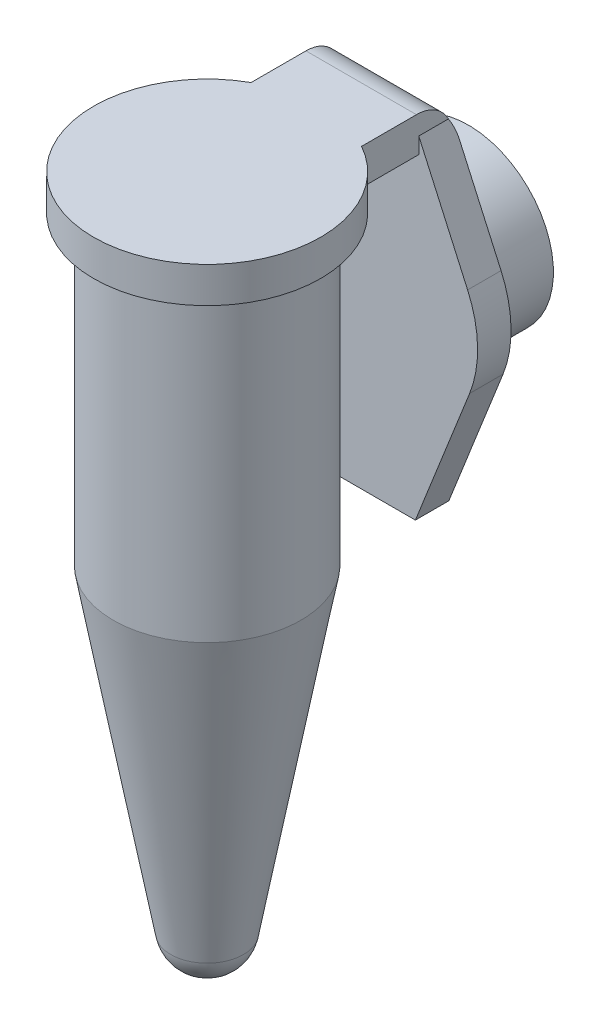
SolidWorks part; units mm, degrees
ref_plane "Front Plane" through (0, 0, 0) normal (0, 0, 1) x (1, 0, 0)
ref_plane "Top Plane" through (0, 0, 0) normal (0, 1, 0) x (1, 0, 0)
ref_plane "Right Plane" through (0, 0, 0) normal (1, 0, 0) x (0, 0, -1)
sketch "Sketch1" plane through (0, 0, 0) normal (0, 0, 1) x (1, 0, 0)
  line L0 (5.25, 36.6) -> (5.25, 19.5)
  line L1 (5.25, 19.5) -> (2.0346, 1.7)
  line L2 (0, 0) -> (0, 38.6)
  line L3 (0, 38.6) -> (6.35, 38.6)
  line L4 (6.35, 38.6) -> (6.35, 36.6)
  line L5 (6.35, 36.6) -> (5.25, 36.6)
  arc A0 (2.0346, 1.7) -> (0, 0) centre (0, 2.0675) cw
  dimension "D1" = 38.6
  dimension "D2" = 2
  dimension "D3" = 17.8
  dimension "D4" = 1.7
  dimension "D5" = 5.25
  dimension "D6" = 6.35
revolve "Revolve1" add sketch "Sketch1" angle 360 about L2
sketch "Sketch2" plane through (0, 38.6, 0) normal (0, 1, 0) x (1, 0, 0)
  line L0 (0, 8.7475) -> (0, 0) construction
  line L1 (-3.09, 5.5475) -> (3.09, 5.5475)
  line L2 (-3.09, 5.5475) -> (-3.09, 8.7475)
  line L3 (-3.09, 8.7475) -> (3.09, 8.7475)
  line L4 (3.09, 5.5475) -> (3.09, 8.7475)
  circle A0 centre (0, 0) radius 6.35 construction
  dimension "D1" = 6.18
  dimension "D2" = 3.2
extrude "Boss-Extrude1" add sketch "Sketch2" against normal blind 2
sketch "Sketch3" plane through (0, 0, -8.7475) normal (0, 0, -1) x (-1, 0, 0)
  line L0 (-2.9, 18.8) -> (2.9, 18.8)
  line L1 (-3.09, 38.6) -> (3.09, 38.6)
  line L2 (-3.09, 38.6) -> (-3.09, 37.5)
  line L4 (3.09, 38.6) -> (3.09, 37.5)
  line L5 (2.9, 18.8) -> (5.9313, 26.4496)
  line L6 (-2.9, 18.8) -> (-5.9313, 26.4496)
  line L7 (-5.8212, 31.4111) -> (-3.09, 37.5)
  line L8 (5.8212, 31.4111) -> (3.09, 37.5)
  line L9 (0, 38.6) -> (0, 18.8) construction
  line L11 (-3.09, 38.6) -> (3.09, 38.6) construction
  arc A0 (5.9313, 26.4496) -> (5.8212, 31.4111) centre (0, 28.8) ccw
  arc A1 (-5.8212, 31.4111) -> (-5.9313, 26.4496) centre (0, 28.8) ccw
  point P6 (0, 0)
  dimension "D1" = 12.76
  dimension "D2" = 10
  dimension "D3" = 1.1
  dimension "D4" = 1.1
  dimension "D5" = 5.8
  dimension "D6" = 8.7
extrude "Boss-Extrude2" add sketch "Sketch3" along normal blind 1.87
sketch "Sketch4" plane through (0, 0, -10.6175) normal (0, 0, -1) x (-1, 0, 0)
  circle A0 centre (0, 28.8) radius 4.75
  circle A1 centre (0, 28.8) radius 3
  dimension "D1" = 9.5
  dimension "D2" = 6
extrude "Boss-Extrude3" add sketch "Sketch4" along normal blind 4
fillet "Fillet1" radius 2 1 edges at (0, 38.6, -10.6175)
